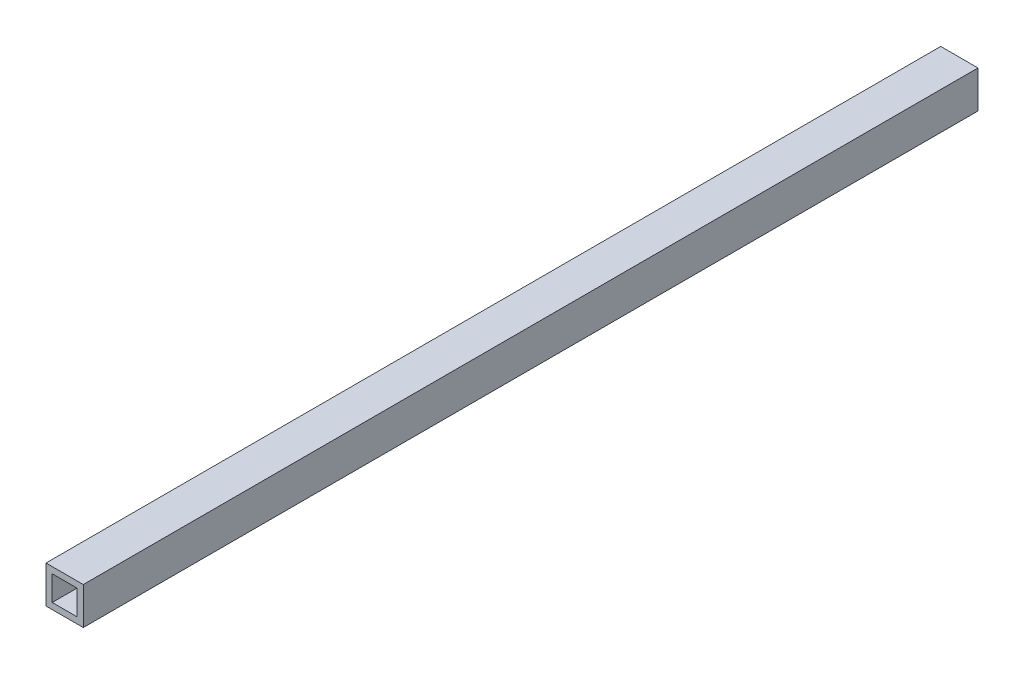
SolidWorks part; units mm, degrees
ref_plane "Front Plane" through (0, 0, 0) normal (0, 0, 1) x (1, 0, 0)
ref_plane "Top Plane" through (0, 0, 0) normal (0, 1, 0) x (1, 0, 0)
ref_plane "Right Plane" through (0, 0, 0) normal (1, 0, 0) x (0, 0, -1)
sketch "Sketch1" plane through (0, 0, 0) normal (0, 0, 1) x (1, 0, 0)
  line L1 (-9.525, -9.525) -> (9.525, -9.525)
  line L2 (-9.525, -9.525) -> (-9.525, 9.525)
  line L3 (-9.525, 9.525) -> (9.525, 9.525)
  line L4 (9.525, -9.525) -> (9.525, 9.525)
  line L5 (-9.525, -9.525) -> (9.525, 9.525) construction
  line L6 (-9.525, 9.525) -> (9.525, -9.525) construction
  point P0 (0, 0)
  dimension "D1" = 19.05
  dimension "D2" = 19.05
extrude "Boss-Extrude1" add sketch "Sketch1" against normal blind 457.2
sketch "Sketch2" plane through (0, 0, 0) normal (0, 0, 1) x (1, 0, 0)
  line L1 (-6.35, -6.35) -> (6.35, -6.35)
  line L2 (-6.35, -6.35) -> (-6.35, 6.35)
  line L3 (-6.35, 6.35) -> (6.35, 6.35)
  line L4 (6.35, -6.35) -> (6.35, 6.35)
  line L5 (-6.35, -6.35) -> (6.35, 6.35) construction
  line L6 (-6.35, 6.35) -> (6.35, -6.35) construction
  point P0 (0, 0)
  dimension "D1" = 12.7
  dimension "D2" = 12.7
extrude "Cut-Extrude1" cut sketch "Sketch2" against normal up to next
equation "\"D2@Sketch1\"=\"D1@Sketch1\""
equation "\"D2@Sketch2\"=\"D1@Sketch2\""
